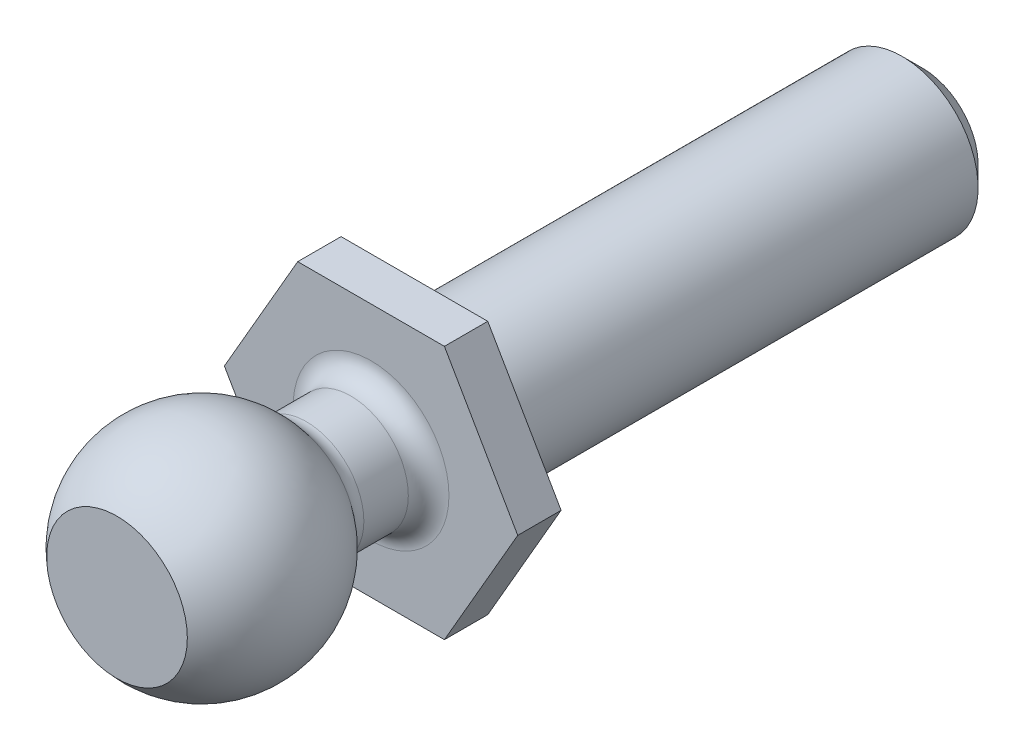
SolidWorks part; units mm, degrees
ref_plane "Front Plane" through (0, 0, 0) normal (0, 0, 1) x (1, 0, 0)
ref_plane "Top Plane" through (0, 0, 0) normal (0, 1, 0) x (1, 0, 0)
ref_plane "Right Plane" through (0, 0, 0) normal (1, 0, 0) x (0, 0, -1)
sketch "Sketch1" plane through (0, 0, 0) normal (0, 0, 1) x (1, 0, 0)
  line L1 (2.7496, 0) -> (1.3748, 2.3812)
  line L2 (1.3748, 2.3812) -> (-1.3748, 2.3812)
  line L3 (-1.3748, 2.3812) -> (-2.7496, 0)
  line L4 (-2.7496, 0) -> (-1.3748, -2.3813)
  line L5 (-1.3748, -2.3813) -> (1.3748, -2.3812)
  line L6 (1.3748, -2.3812) -> (2.7496, 0)
  circle A0 centre (0, 0) radius 2.3813 construction
  dimension "D1" = 4.7625
extrude "Boss-Extrude1" add sketch "Sketch1" along normal blind 0.8128
sketch "Sketch2" plane through (0, 0, 0.8128) normal (0, 0, 1) x (1, 0, 0)
  circle A0 centre (0, 0) radius 1.0795
  dimension "D1" = 2.159
extrude "Boss-Extrude2" add sketch "Sketch2" along normal blind 3.175
sketch "Sketch3" plane through (0, 0, 3.9878) normal (0, 0, 1) x (1, 0, 0)
  line L0 (0, 2.0638) -> (0, -2.0638) construction
  circle A0 centre (0, 0) radius 2.0638
  dimension "D1" = 4.1275
revolve "Revolve2" add sketch "Sketch3" angle 360 about L0
fillet "Fillet1" radius 0.381 2 edges at (1.0795, 0, 2.2289) (1.0795, 0, 0.8128)
sketch "Sketch4" plane through (0, 0, 0) normal (0, 0, -1) x (-1, 0, 0)
  circle A0 centre (0, 0) radius 1.4224
  dimension "D1" = 2.8448
extrude "Boss-Extrude3" add sketch "Sketch4" along normal blind 9.525
cosmetic thread "Cosmetic Thread1" parameters "D2"=2.0879
chamfer "Chamfer1" distance 0.381 1 edges at (-1.4224, 0, -9.525)
ref_plane "Plane1" through (0, 0, 5.5753) normal (0, 0, 1) x (1, 0, 0)
split "Split1" trim tools "Plane1" bodies to split 104 resulting bodies 105
